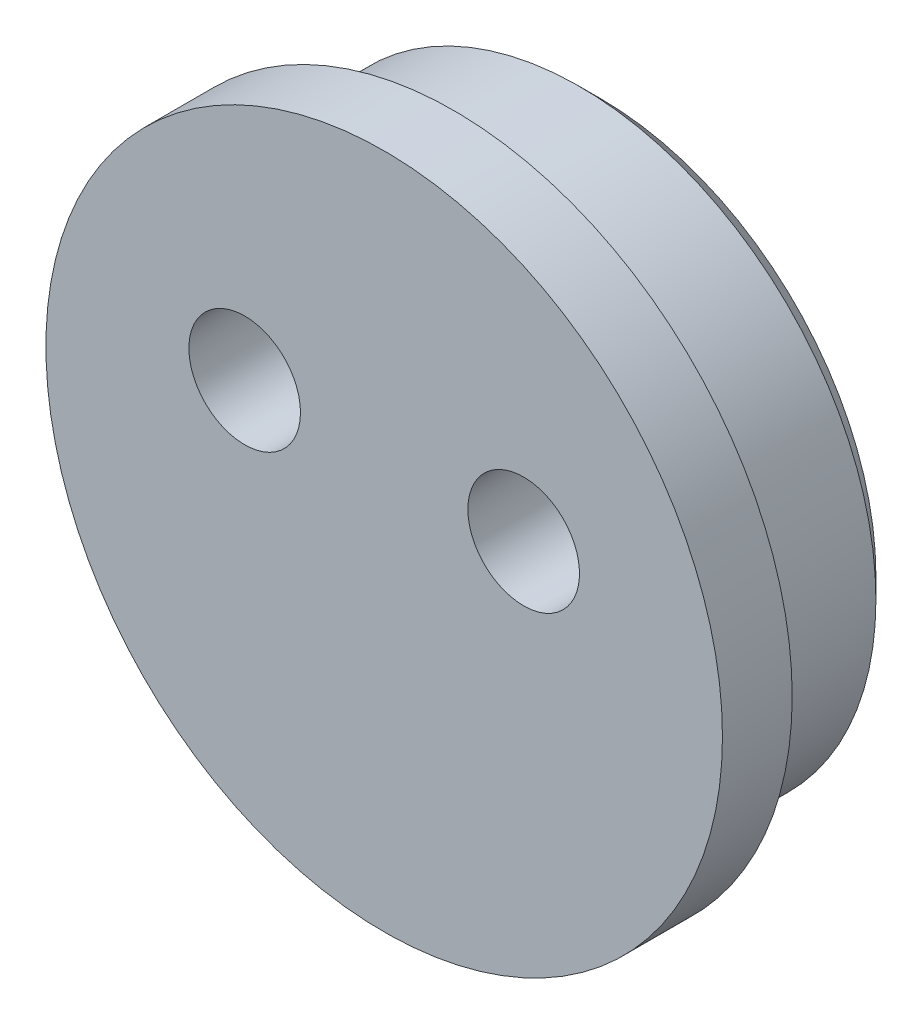
SolidWorks part; units mm, degrees
material "ABS"
ref_plane "Plan de face" through (0, 0, 0) normal (0, 0, 1) x (1, 0, 0)
ref_plane "Plan de dessus" through (0, 0, 0) normal (0, 1, 0) x (1, 0, 0)
ref_plane "Plan de droite" through (0, 0, 0) normal (1, 0, 0) x (0, 0, -1)
sketch "Esquisse1" plane through (0, 0, 0) normal (0, 0, 1) x (1, 0, 0)
  line L0 (0, 0) -> (0, 8.5) construction
  circle A0 centre (0, 0) radius 8.5
  circle A1 centre (-4, 2) radius 1.6
  circle A2 centre (4, 2) radius 1.6
  dimension "D1" = 17
  dimension "D2" = 3.2
  dimension "D3" = 8
  dimension "D4" = 2
extrude "Boss.-Extru.1" add sketch "Esquisse1" along normal blind 6.2
sketch "Esquisse2" plane through (0, 0, 6.2) normal (0, 0, 1) x (1, 0, 0)
  circle A0 centre (0, 0) radius 9.7
  circle A1 centre (0, 0) radius 8.5 construction
  circle A2 centre (0, 0) radius 8.5
  dimension "D1" = 1.2
extrude "Boss.-Extru.2" add sketch "Esquisse2" against normal blind 2
chamfer "Chanfrein1" distance 0.6 angle 45 1 edges at (8.5, 0, 0)
